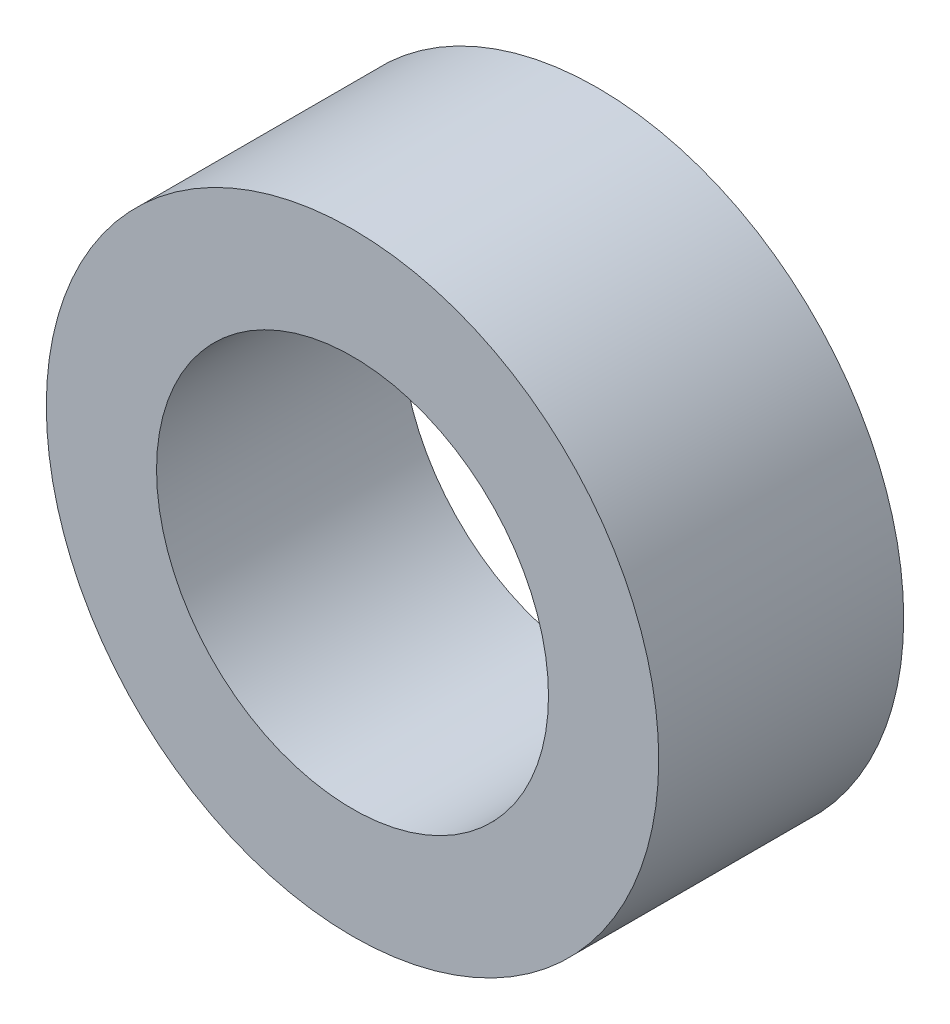
SolidWorks part; units mm, degrees
ref_plane "Front Plane" through (0, 0, 0) normal (0, 0, 1) x (1, 0, 0)
ref_plane "Top Plane" through (0, 0, 0) normal (0, 1, 0) x (1, 0, 0)
ref_plane "Right Plane" through (0, 0, 0) normal (1, 0, 0) x (0, 0, -1)
sketch "Sketch1" plane through (0, 0, 0) normal (0, 0, 1) x (1, 0, 0)
  circle A0 centre (0, 0) radius 3.2
  circle A1 centre (0, 0) radius 5
extrude "Boss-Extrude1" add sketch "Sketch1" along normal blind 4
